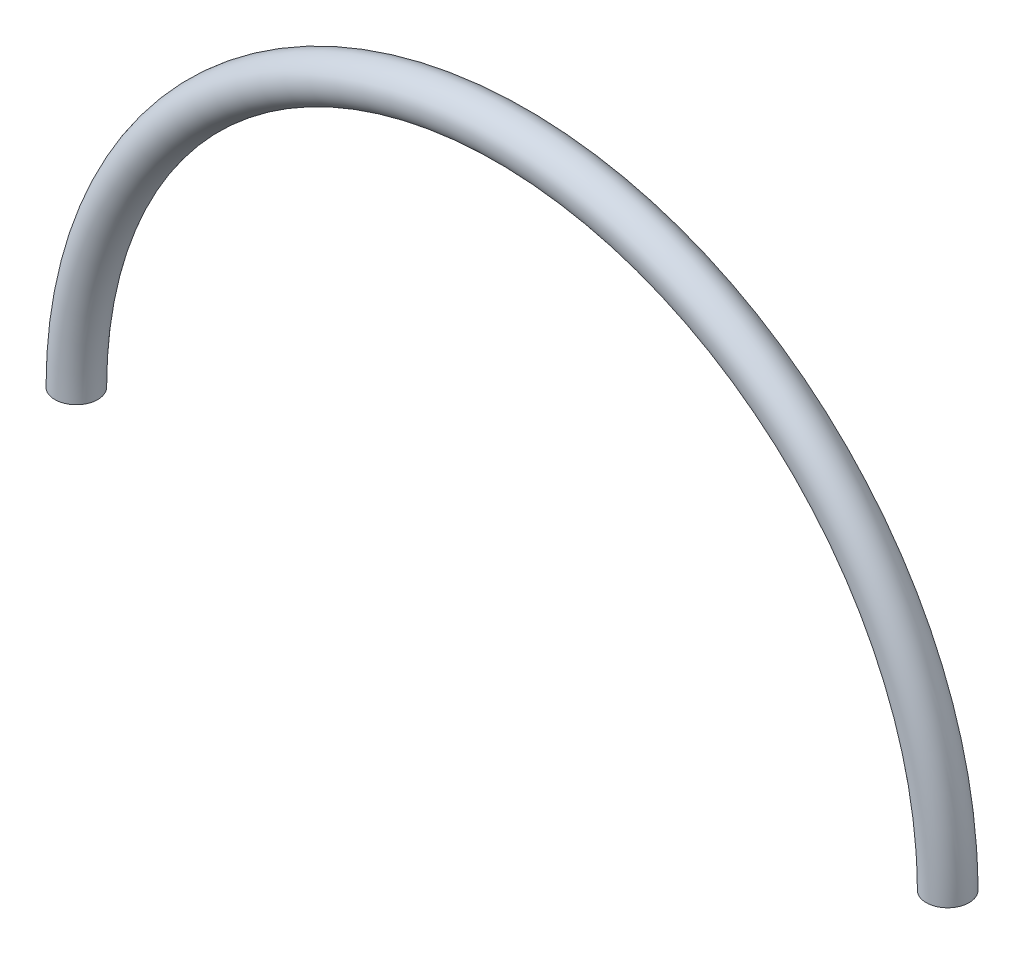
SolidWorks part; units mm, degrees
ref_plane "Front Plane" through (0, 0, 0) normal (0, 0, 1) x (1, 0, 0)
ref_plane "Top Plane" through (0, 0, 0) normal (0, 1, 0) x (1, 0, 0)
ref_plane "Right Plane" through (0, 0, 0) normal (1, 0, 0) x (0, 0, -1)
sketch "Sketch1" plane through (0, 0, 0) normal (0, 1, 0) x (1, 0, 0)
  line L0 (0, 0) -> (129, 0) construction
sketch "Sketch2" plane through (0, 0, 0) normal (0, 0, 1) x (1, 0, 0)
  line L0 (0, 0) -> (129, 0) construction
  arc A0 (0, 0) -> (129, 0) centre (64.5, 0) cw
ref_plane "Plane1" through (0, 0, 0) normal (0, 1, 0) x (1, 0, 0)
sketch "Sketch3" plane through (0, 0, 0) normal (0, 1, 0) x (1, 0, 0)
  circle A0 centre (0, 0) radius 3.175
sweep "Sweep1" add profiles "Sketch3" path "Sketch2"
